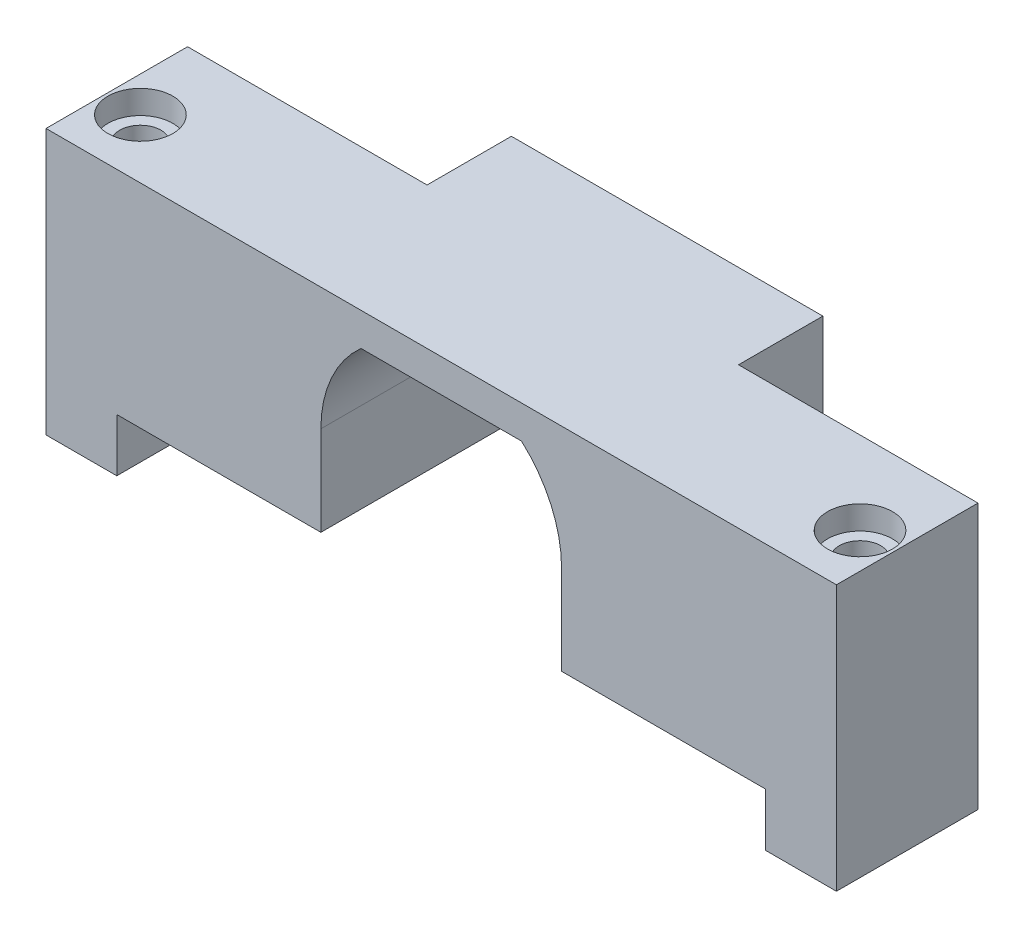
SolidWorks part; units mm, degrees
ref_plane "Front Plane" through (0, 0, 0) normal (0, 0, 1) x (1, 0, 0)
ref_plane "Top Plane" through (0, 0, 0) normal (0, 1, 0) x (1, 0, 0)
ref_plane "Right Plane" through (0, 0, 0) normal (1, 0, 0) x (0, 0, -1)
sketch "Sketch1" plane through (0, 0, 0) normal (0, 0, 1) x (1, 0, 0)
  line L0 (27.5, 0) -> (27.5, 18) construction
  line L1 (0, 0) -> (17.3, 0)
  line L2 (0, 0) -> (0, 18)
  line L3 (0, 18) -> (55, 18)
  line L4 (55, 0) -> (55, 18)
  line L5 (20.6971, 15.2) -> (34.3029, 15.2)
  line L7 (17.3, 0) -> (17.3, 7.6)
  line L8 (37.7, 0) -> (37.7, 7.6)
  line L9 (20.6971, 15.2) -> (34.3029, 15.2)
  line L10 (17.3, 0) -> (37.7, 15.2) construction
  line L11 (17.3, 15.2) -> (37.7, 0) construction
  line L12 (0, 15.2) -> (55, 15.2) construction
  line L13 (37.7, 0) -> (55, 0)
  line L14 (0, 0) -> (55, 0) construction
  line L15 (17.3, 7.6) -> (17.3, 15.2)
  line L16 (17.3, 15.2) -> (37.7, 15.2)
  line L17 (37.7, 15.2) -> (37.7, 7.6)
  arc A2 (20.6971, 15.2) -> (17.3, 7.6) centre (27.5, 7.6) ccw
  arc A3 (37.7, 7.6) -> (34.3029, 15.2) centre (27.5, 7.6) ccw
  dimension "D3" = 10.2
  dimension "D6" = 20.4
  dimension "D1" = 55
  dimension "D2" = 18
  dimension "D5" = 10.2
  dimension "D4" = 15.2
extrude "Boss-Extrude2" add sketch "Sketch1" along normal blind 12 contours L16 L17 L8 L13 L4 L3 L2 L1 L7 L15 L5 | A2 L16 L15 | A3 L17 L16
sketch "Sketch2" plane through (0, 0, 0) normal (-1, 0, 0) x (0, 0, 1)
  line L0 (12, 0) -> (12, 18) construction
  line L5 (12, 0) -> (0, 0) construction
  line L6 (0, 18) -> (12, 18)
  line L7 (0, 18) -> (0, -4.5)
  line L8 (0, -4.5) -> (12, -4.5)
  line L9 (12, 18) -> (12, -4.5)
  dimension "D1" = 4.5
extrude "Boss-Extrude3" add sketch "Sketch2" along normal blind 6
sketch "Sketch3" plane through (55, 0, 0) normal (1, 0, 0) x (0, 0, -1)
  line L1 (-12, 18) -> (0, 18)
  line L2 (-12, 18) -> (-12, -4.5)
  line L3 (-12, -4.5) -> (0, -4.5)
  line L4 (0, 18) -> (0, -4.5)
extrude "Boss-Extrude4" add sketch "Sketch3" along normal blind 6
sketch "Sketch4" plane through (0, 18, 0) normal (0, 1, 0) x (1, 0, 0)
  line L0 (0, 0) -> (0, -12) construction
  line L1 (-6, -12) -> (-6, 0) construction
  line L3 (27.5, 0) -> (27.5, -12) construction
  line L4 (-6, 0) -> (61, 0) construction
  line L5 (-6, -12) -> (61, -12) construction
  line L6 (0, 0) -> (0, -12) construction
  circle A0 centre (-3, -7) radius 1.75
  circle A1 centre (58, -7) radius 1.75
  dimension "D1" = 3.5
  dimension "D2" = 3
  dimension "D3" = 5
extrude "Cut-Extrude1" cut sketch "Sketch4" against normal up to surface (22.5 mm away) up to face at (-3, -4.5, 6)
sketch "Sketch5" plane through (0, 0, 0) normal (0, 0, -1) x (-1, 0, 0)
  line L0 (-37.7, 7.6) -> (-17.3, 7.6) construction
  line L1 (-37.7, 0) -> (-40.7, 0)
  line L2 (-37.7, 0) -> (-55, 0) construction
  line L3 (-40.7, 0) -> (-40.7, 18)
  line L4 (6, 18) -> (-61, 18) construction
  line L5 (-40.7, 18) -> (-14.3, 18)
  line L6 (-27.5, 18) -> (-27.5, 0) construction
  line L7 (-17.3, 6) -> (-17.3, 0)
  line L8 (-20.6971, 15.2) -> (-34.3029, 15.2) construction
  line L9 (-37.7, 7.6) -> (-37.7, 0) construction
  line L10 (-20.6971, 15.2) -> (-34.3029, 15.2)
  line L11 (-37.7, 6) -> (-37.7, 0)
  line L12 (-14.3, 0) -> (-14.3, 18)
  line L13 (-17.3, 0) -> (-14.3, 0)
  arc A0 (-37.7, 6) -> (-37.5745, 9.1951) centre (-37.7, 7.6) ccw
  arc A1 (-34.3029, 15.2) -> (-37.7, 7.6) centre (-27.5, 7.6) ccw construction
  arc A2 (-34.3029, 15.2) -> (-37.5745, 9.1951) centre (-27.5, 7.6) ccw
  arc A3 (-20.6971, 15.2) -> (-17.4255, 9.1951) centre (-27.5, 7.6) cw
  arc A4 (-17.3, 6) -> (-17.4255, 9.1951) centre (-17.3, 7.6) cw
  point P22 (-27.5, 15.2)
  dimension "D1" = 3.2
  dimension "D2" = 3
extrude "Boss-Extrude5" add sketch "Sketch5" along normal blind 4.65
sketch "Sketch6" plane through (0, 0, -4.65) normal (0, 0, -1) x (-1, 0, 0)
  line L0 (-27.5, 18) -> (-27.5, 0) construction
  line L1 (-14.3, 18) -> (-40.7, 18) construction
  line L2 (-36.1012, 7.5372) -> (-18.8988, 7.5372) construction
  line L3 (-40.7, 18) -> (-40.7, 0)
  line L4 (-40.7, 0) -> (-37.7, 0) construction
  line L5 (-40.7, 18) -> (-40.7, 0) construction
  line L6 (-40.7, 0) -> (-14.3, 0)
  line L7 (-17.3, 0) -> (-14.3, 0) construction
  line L8 (-14.3, 0) -> (-14.3, 18)
  line L9 (-14.3, 18) -> (-40.7, 18)
  arc A0 (-37.7, 6) -> (-37.5745, 9.1951) centre (-37.7, 7.6) ccw construction
  arc A1 (-17.4255, 9.1951) -> (-17.3, 6) centre (-17.3, 7.6) ccw construction
  circle A2 centre (-27.5, 7.5372) radius 4.925
  dimension "D1" = 9.85
extrude "Boss-Extrude6" add sketch "Sketch6" along normal blind 2.5
sketch "Sketch7" plane through (0, 18, 0) normal (0, 1, 0) x (1, 0, 0)
  circle A0 centre (-3, -7) radius 2.75
  circle A1 centre (58, -7) radius 2.75
  dimension "D1" = 5.5
  dimension "D2" = 5.5
extrude "Cut-Extrude2" cut sketch "Sketch7" against normal blind 2
